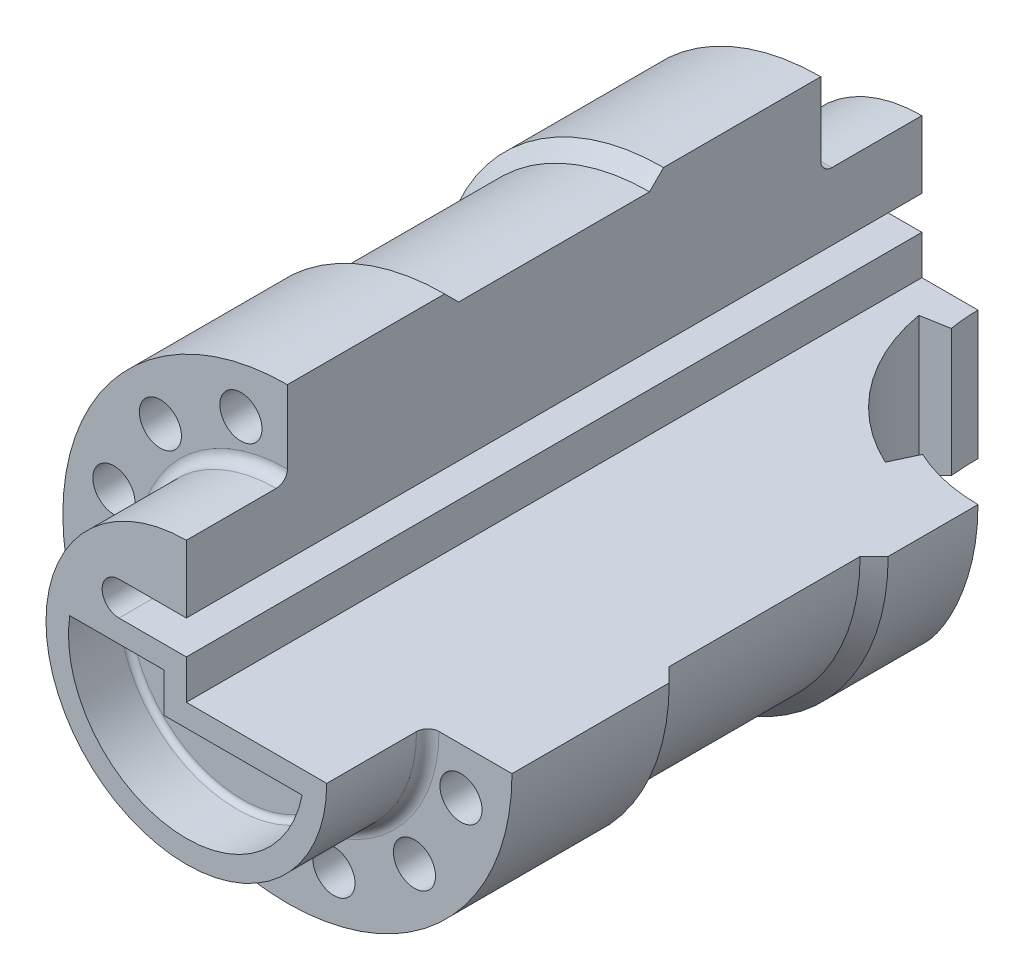
SolidWorks part; units mm, degrees
material "AISI 1020"
ref_plane "Front Plane" through (0, 0, 0) normal (0, 0, 1) x (1, 0, 0)
ref_plane "Top Plane" through (0, 0, 0) normal (0, 1, 0) x (1, 0, 0)
ref_plane "Right Plane" through (0, 0, 0) normal (1, 0, 0) x (0, 0, -1)
sketch "Sketch1" plane through (0, 0, 0) normal (1, 0, 0) x (0, 0, -1)
  line L0 (0, 33.8319) -> (0, -14.886) construction
  line L1 (65.5, 0) -> (-65.5, 0)
  line L2 (-65.5, 0) -> (-65.5, 25)
  line L3 (-65.5, 25) -> (-49.5, 25)
  line L4 (-47.5, 40) -> (-47.5, 27)
  line L5 (-47.5, 40) -> (-19.5, 40)
  line L6 (-19.5, 40) -> (-17, 37.5)
  line L7 (-17, 37.5) -> (17, 37.5)
  line L8 (65.5, 0) -> (65.5, 25)
  line L9 (65.5, 25) -> (49.5, 25)
  line L10 (47.5, 40) -> (47.5, 27)
  line L11 (47.5, 40) -> (19.5, 40)
  line L12 (19.5, 40) -> (17, 37.5)
  arc A0 (-49.5, 25) -> (-47.5, 27) centre (-49.5, 27) ccw
  arc A1 (49.5, 25) -> (47.5, 27) centre (49.5, 27) cw
  point P12 (0, 0)
  point P17 (0, 37.5)
  point P19 (-47.5, 25)
  point P22 (47.5, 25)
  dimension "D3" = 2
  dimension "D4" = 2
  dimension "D1" = 25
  dimension "D2" = 40
  dimension "D5" = 18
  dimension "D6" = 28
  dimension "D7" = 2.5
  dimension "D8" = 45
  dimension "D9" = 131
revolve "Revolve1" add sketch "Sketch1" angle 360 about L1
sketch "Sketch2" plane through (0, 0, 0) normal (0, 0, 1) x (1, 0, 0)
  line L0 (0, 40) -> (0, 13)
  line L1 (0, 0) -> (40, 0)
  line L2 (-12, 10) -> (3.2622, 10) construction
  line L3 (-12, 13) -> (0, 13)
  line L4 (-12, 7) -> (0, 7)
  line L5 (0, 7) -> (0, 0)
  circle A1 centre (0, 0) radius 40 construction
  arc A2 (-12, 13) -> (-12, 7) centre (-12, 10) ccw
  arc A4 (0, 40) -> (40, 0) centre (0, 0) cw
  point P8 (-4.3689, 10)
  dimension "D2" = 3
  dimension "D1" = 7
  dimension "D3" = 12
extrude "Cut-Extrude1" cut sketch "Sketch2" against normal through all both and the other way through all
sketch "Sketch3" plane through (0, 0, 0) normal (0, 1, 0) x (1, 0, 0)
  line L0 (27.3215, 38.3108) -> (25.2084, 33.7792)
  line L1 (10.4558, 60.2906) -> (5.5317, 59.4223)
  line L2 (25, 49.5) -> (25, 65.5) construction
  line L3 (25, 65.5) -> (-25, 65.5) construction
  line L4 (25, 65.5) -> (44.4611, 65.5) construction
  line L5 (40, 47.5) -> (40, 77.2344) construction
  arc A0 (5.5317, 59.4223) -> (25.2084, 33.7792) centre (40, 65.5) ccw
  arc A1 (27.3215, 38.3108) -> (10.4558, 60.2906) centre (40, 65.5) ccw
  point P17 (40, 65.5)
  point P18 (0, 0)
  point P19 (0, 0)
  point P20 (38.3608, 66.7473)
  dimension "D1" = 35
  dimension "D2" = 30
  dimension "D3" = 25
  dimension "D4" = 10
extrude "Cut-Extrude3" cut sketch "Sketch3" against normal through all
sketch "Sketch4" plane through (0, 0, 0) normal (0, 0, 1) x (1, 0, 0)
  line L0 (-8.2822, 30.9096) -> (0, 0) construction
  line L1 (0, 0) -> (0, 32) construction
  circle A0 centre (0, 0) radius 32 construction
  circle A1 centre (-8.2822, 30.9096) radius 3.75
  circle A2 centre (8.2822, 30.9096) radius 3.75
  circle A3 centre (22.6274, 22.6274) radius 3.75
  circle A4 centre (30.9096, 8.2822) radius 3.75
  circle A5 centre (30.9096, -8.2822) radius 3.75
  circle A6 centre (22.6274, -22.6274) radius 3.75
  circle A7 centre (8.2822, -30.9096) radius 3.75
  circle A8 centre (-8.2822, -30.9096) radius 3.75
  circle A9 centre (-22.6274, -22.6274) radius 3.75
  circle A10 centre (-30.9096, -8.2822) radius 3.75
  circle A11 centre (-30.9096, 8.2822) radius 3.75
  circle A12 centre (-22.6274, 22.6274) radius 3.75
  point P31 (0, 0)
  dimension "D1" = 7.5
  dimension "D3" = 64
  dimension "D2" = 15
  dimension "D4" = 12
extrude "Cut-Extrude4" cut sketch "Sketch4" against normal through all both and the other way through all
sketch "Sketch5" plane through (0, 0, 65.5) normal (0, 0, 1) x (1, 0, 0)
  line L0 (-20.7846, 3) -> (-4, 3)
  line L1 (-4, 3) -> (-4, -4)
  line L2 (-4, -4) -> (20.6155, -4)
  line L3 (-12, 7) -> (0, 7) construction
  line L4 (0, 7) -> (0, 0) construction
  line L5 (0, 0) -> (25, 0) construction
  arc A0 (20.6155, -4) -> (-20.7846, 3) centre (0, 0) cw
  arc A1 (0, 25) -> (25, 0) centre (0, 0) ccw construction
  point P8 (-4, -0.5)
  dimension "D4" = 4
  dimension "D1" = 4
  dimension "D2" = 4
  dimension "D3" = 4
extrude "Cut-Extrude5" cut sketch "Sketch5" against normal blind 10
fillet "Fillet1" radius 1 4 edges at (8.3078, -4, 55.5) (-4, -0.5, 55.5) (-12.3923, 3, 55.5) (-3.501, -20.7061, 55.5)
equation "\"A\"= 131"
equation "\"B\"= 18"
equation "\"C\"= 28"
equation "\"D5@Sketch1\"=\"B\""
equation "\"D6@Sketch1\"=\"C\""
equation "\"D9@Sketch1\"=\"A\""
